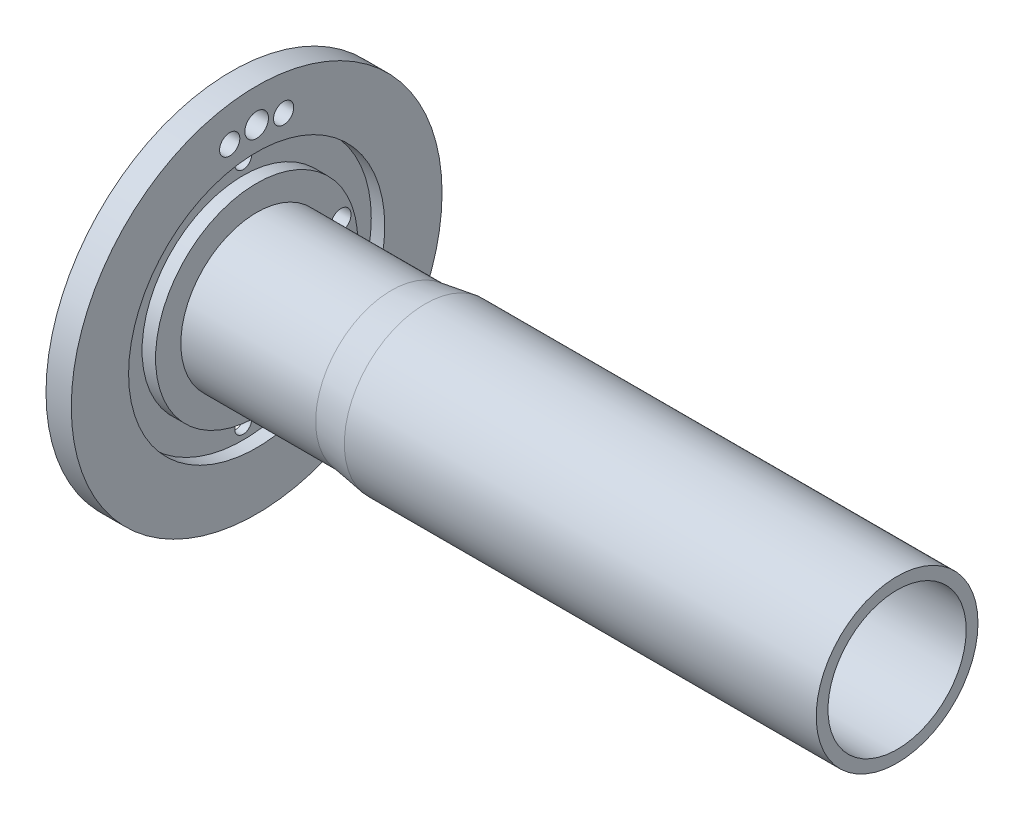
SolidWorks part; units mm, degrees
ref_plane "Front Plane" through (0, 0, 0) normal (0, 0, 1) x (1, 0, 0)
ref_plane "Top Plane" through (0, 0, 0) normal (0, 1, 0) x (1, 0, 0)
ref_plane "Right Plane" through (0, 0, 0) normal (1, 0, 0) x (0, 0, -1)
sketch "Sketch2" plane through (0, 0, 0) normal (1, 0, 0) x (0, 0, -1)
  circle A0 centre (0, 0) radius 55
extrude "Boss-Extrude1" add sketch "Sketch2" along normal blind 10
sketch "Sketch3" plane through (10, 0, 0) normal (1, 0, 0) x (0, 0, -1)
  circle A0 centre (0, 0) radius 22.5
extrude "Boss-Extrude2" add sketch "Sketch3" along normal blind 40
sketch "Sketch4" plane through (0, 0, 0) normal (-1, 0, 0) x (0, 0, 1)
  circle A0 centre (0, 0) radius 19
extrude "Cut-Extrude1" cut sketch "Sketch4" against normal through all both and the other way through all
sketch "Sketch14" plane through (0, 0, 0) normal (-1, 0, 0) x (0, 0, 1)
  circle A0 centre (0, 0) radius 30.5
  circle A1 centre (0, 0) radius 37.5
sketch "Sketch15" plane through (10, 0, 0) normal (1, 0, 0) x (0, 0, -1)
  circle A0 centre (0, 0) radius 30
  circle A1 centre (0, 0) radius 38
extrude "Cut-Extrude5" cut sketch "Sketch14" against normal blind 3
extrude "Cut-Extrude6" cut sketch "Sketch15" against normal blind 4
sketch "Sketch16" plane through (0, 0, 0) normal (-1, 0, 0) x (0, 0, 1)
  circle A0 centre (0, 34) radius 2.5
  circle A1 centre (0, -34) radius 2.5
extrude "Cut-Extrude7" cut sketch "Sketch16" against normal through all
sketch "Sketch17" plane through (0, 0, 0) normal (-1, 0, 0) x (0, 0, 1)
  circle A0 centre (0, -34) radius 5
  circle A1 centre (0, 34) radius 5
extrude "Cut-Extrude8" cut sketch "Sketch17" against normal blind 3.7
sketch "Sketch20" plane through (0, 0, 0) normal (-1, 0, 0) x (0, 0, 1)
  circle A0 centre (-26, 0) radius 3.5
  circle A1 centre (-25, -8) radius 3
  circle A2 centre (-25, 8) radius 3
  point P2 (0, 0)
extrude "Cut-Extrude9" cut sketch "Sketch20" against normal blind 10
sketch "Sketch21" plane through (0, 0, 0) normal (-1, 0, 0) x (0, 0, 1)
  circle A0 centre (0, 45) radius 3.5
  circle A1 centre (-8, 44) radius 3
  circle A2 centre (8, 44) radius 3
  point P2 (0, 0)
  point P5 (0, 0)
  point P8 (0, 0)
extrude "Cut-Extrude10" cut sketch "Sketch21" against normal blind 10
ref_plane "Plane1" through (60, 0, 0) normal (1, 0, 0) x (0, 0, -1)
sketch "Sketch22" plane through (60, 0, 0) normal (1, 0, 0) x (0, 0, -1)
  circle A0 centre (0, 0) radius 24
extrude "Boss-Extrude3" add sketch "Sketch22" along normal blind 140 separate body contours A0
sketch "Sketch23" plane through (200, 0, 0) normal (1, 0, 0) x (0, 0, -1)
  circle A0 centre (0, 0) radius 20.5
extrude "Cut-Extrude11" cut sketch "Sketch23" against normal up to next (140 mm away)
loft "Loft5" add section edge at (60, 0, -24) section edge at (50, 0, -22.5)
loft "Cut-Loft1" cut section edge at (60, 0, -20.5) section edge at (50, 0, 19)
sketch "Sketch25" plane through (0, 0, 0) normal (-1, 0, 0) x (0, 0, 1)
  circle A0 centre (0, 0) radius 103.9725
extrude "Cut-Extrude12" cut sketch "Sketch25" against normal blind 2.5
